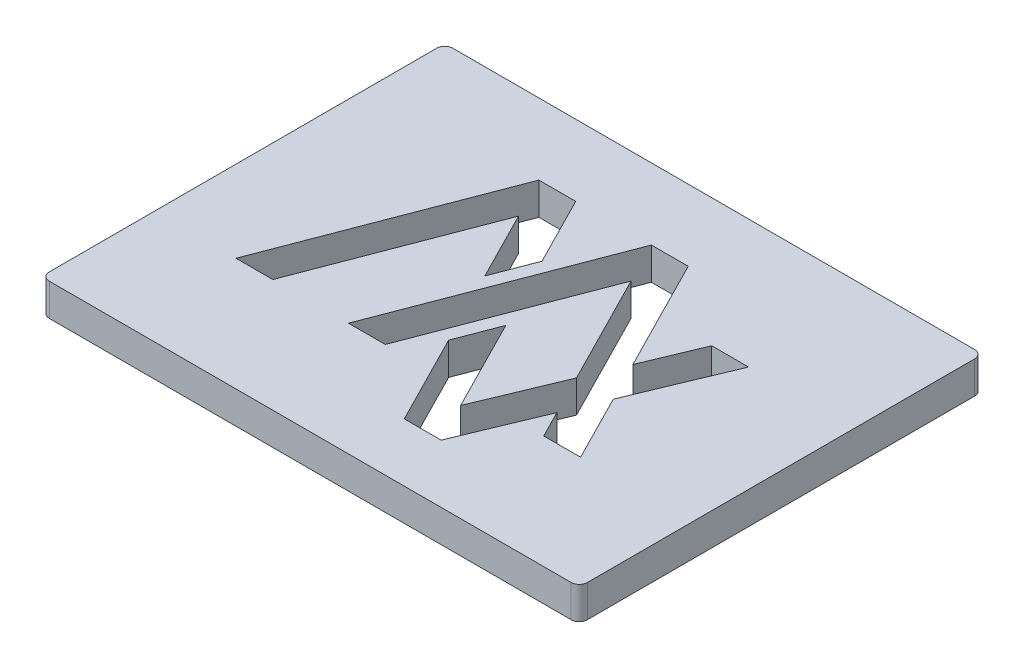
SolidWorks part; units mm, degrees
ref_plane "前视基准面" through (0, 0, 0) normal (0, 0, 1) x (1, 0, 0)
ref_plane "上视基准面" through (0, 0, 0) normal (0, 1, 0) x (1, 0, 0)
ref_plane "右视基准面" through (0, 0, 0) normal (1, 0, 0) x (0, 0, -1)
sketch "Sketch1" plane through (0, 0, 0) normal (0, 1, 0) x (1, 0, 0)
  line L1 (-97, -75) -> (97, -75)
  line L2 (-100, -72) -> (-100, 72)
  line L3 (-97, 75) -> (97, 75)
  line L4 (100, -72) -> (100, 72)
  line L5 (-100, -75) -> (100, 75) construction
  line L6 (-100, 75) -> (100, -75) construction
  arc A0 (97, 75) -> (100, 72) centre (97, 72) cw
  arc A1 (97, -75) -> (100, -72) centre (97, -72) ccw
  arc A2 (-97, -75) -> (-100, -72) centre (-97, -72) cw
  arc A3 (-100, 72) -> (-97, 75) centre (-97, 72) cw
  point P0 (0, 0)
  dimension "D3" = 3
  dimension "D1" = 150
  dimension "D2" = 200
extrude "Boss-Extrude1" add sketch "Sketch1" along normal blind 12
sketch "Sketch2" plane through (0, 12, 0) normal (0, 1, 0) x (1, 0, 0)
  line L0 (-69.6952, -32.9244) -> (-55.9952, -32.9244)
  line L5 (-11.857, 23.007) -> (-17.733, 7.6329)
  line L6 (2.0809, -4.3809) -> (-3.7951, -19.7551)
  line L7 (-69.6952, -32.9244) -> (-38.5559, 48.5499)
  line L8 (-55.9952, -32.9244) -> (-30.7319, 33.1758)
  line L9 (-38.5559, 48.5499) -> (-24.8559, 48.5499)
  line L10 (-38.5559, 48.5499) -> (-24.8559, 48.5499)
  line L11 (-30.7319, 33.1758) -> (-17.733, 7.6329)
  line L12 (-24.8559, 48.5499) -> (-11.857, 23.007)
  line L13 (13.2988, -53.3445) -> (26.9988, -53.3445)
  line L14 (13.2988, -53.3445) -> (26.9988, -53.3445)
  line L15 (19.4645, -38.5396) -> (32.1172, -8.158)
  line L16 (26.9988, -53.3445) -> (39.6515, -22.963)
  line L17 (46.8993, 27.3362) -> (60.5993, 27.3362)
  line L18 (-27.8811, -32.9244) -> (-14.1811, -32.9244)
  line L19 (-27.8811, -32.9244) -> (3.2582, 48.5499)
  line L20 (-14.1811, -32.9244) -> (11.0822, 33.1758)
  line L21 (3.2582, 48.5499) -> (16.9582, 48.5499)
  line L22 (3.2582, 48.5499) -> (16.9582, 48.5499)
  line L23 (11.0822, 33.1758) -> (32.1172, -8.158)
  line L24 (16.9582, 48.5499) -> (38.2829, 6.6469)
  line L25 (44.721, -32.9244) -> (58.421, -32.9244)
  line L26 (2.0809, -4.3809) -> (19.4645, -38.5396)
  line L27 (-3.7951, -19.7551) -> (13.2988, -53.3445)
  line L28 (39.6515, -22.963) -> (44.721, -32.9244)
  line L29 (45.8172, -8.158) -> (58.421, -32.9244)
  line L30 (38.2829, 6.6469) -> (46.8993, 27.3362)
  line L31 (45.8172, -8.158) -> (60.5993, 27.3362)
  point P0 (-11.8982, 5.3225)
  point P5 (-14.795, 15.32)
  point P17 (10.1082, 48.5499)
  dimension "D1" = 13.7
  dimension "D2" = 5
  dimension "D3" = 5
extrude "Cut-Extrude1" cut sketch "Sketch2" against normal blind 12 contours L12 L9 L7 L0 L8 L11 L5 | L29 L31 L17 L30 L24 L21 L19 L18 L20 L23 L15 L26 L6 L27 L13 L16 L28 L25
